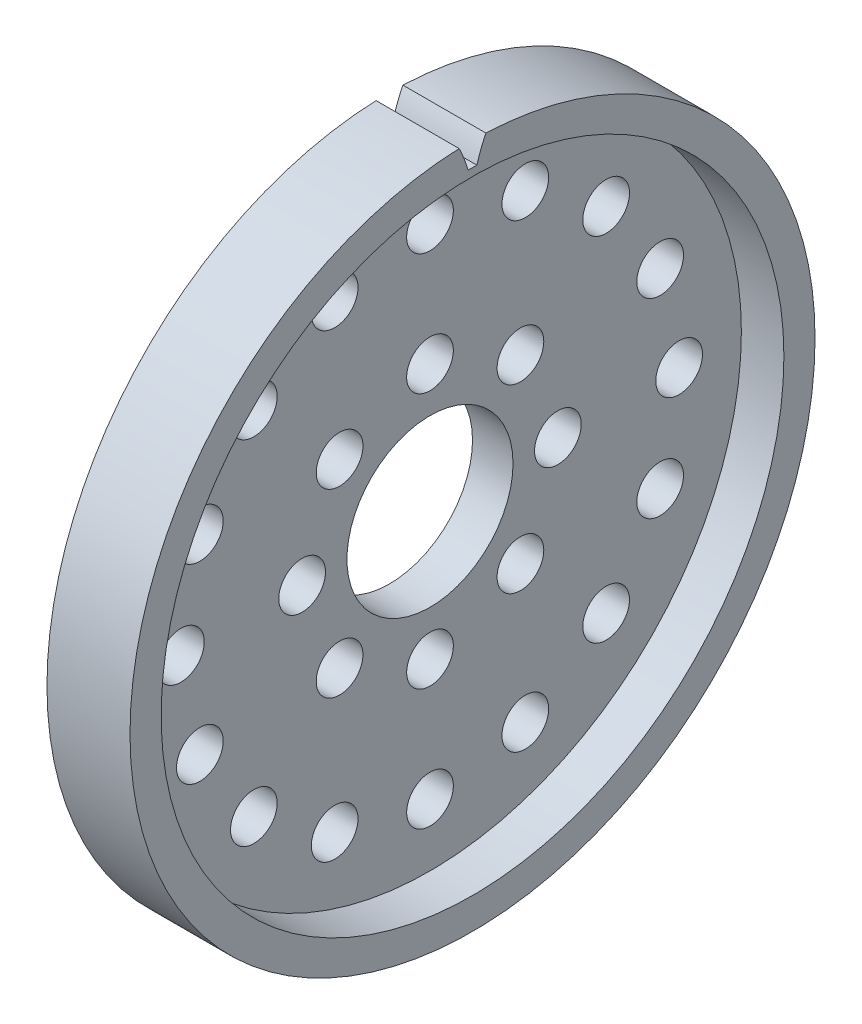
SolidWorks part; units mm, degrees
material "7075-O (SS)"
ref_plane "Plane1" through (0, 0, 0) normal (0, 0, 1) x (1, 0, 0)
ref_plane "Plane2" through (0, 0, 0) normal (0, 1, 0) x (1, 0, 0)
ref_plane "Plane3" through (0, 0, 0) normal (1, 0, 0) x (0, 0, -1)
sketch "HoldingSke" plane through (0, 0, 0) normal (0, 1, 0) x (1, 0, 0)
  line L0 (0, 0) -> (356.3081, -730.5398)
  line L1 (-15, 0) -> (100, 0) construction
  line L2 (0, 0) -> (-2.1039, 2.3779)
  line L3 (0, 0) -> (-11.863, 4.5341)
  line L4 (0, 0) -> (3.7858, 7.762)
  line L5 (0, 0) -> (-47.5972, -17.7524)
  line L6 (0, 0) -> (-5.2639, -3.5516)
  line L7 (-2.1039, 2.3779) -> (8.8308, 51.9871)
  line L8 (-76.2, 54.61) -> (-61.976, 54.61)
  line L9 (-71.009, 38.7566) -> (-53.1078, 45.2721)
  line L10 (-76.2, 71.12) -> (104.1128, 71.12)
  line L11 (0, 0) -> (-6.35, 0)
  line L12 (-76.2, 101.6) -> (-76.1716, 101.6)
  line L13 (24.9733, 27.94) -> (52.9518, 28.4284)
  line L14 (24.9733, 27.94) -> (25.0241, 27.9398)
  line L15 (24.9733, 27.94) -> (100.4021, 29.52)
  circle A0 centre (0, 0) radius 6.35
  circle A1 centre (0, 0) radius 24.3967
  circle A2 centre (0, 0) radius 38.1
  circle A3 centre (0, 0) radius 6.35
  dimension "MHD" = 48.7934
  dimension "Hub_dia" = 76.2
  dimension "Bore" = 12.7
  dimension "MBD" = 12.7
  dimension "Num_teeth" = 64
  dimension "Pitch_radius" = 180.3128
  dimension "Pitch" = 812.8
  dimension "Width" = 6.35
  dimension "Overall_len" = 50.8
  dimension "Show_teeth" = 64
  dimension "Thickness" = 6.35
  dimension "OAL" = 50.8001
  dimension "T_dim" = 14.224
  dimension "Ap" = 20
  dimension "H" = 19.05
  dimension "Backlash" = 0.0284
  dimension "Addendum_fac" = 1
  dimension "Dedendum_fac" = 1.2
  dimension "Clearance_fac" = 0.2
  dimension "Dedendum_add" = 0.0508
sketch "BasProSke" plane through (0, 0, 0) normal (0, 1, 0) x (1, 0, 0)
  line L0 (-10, 0) -> (60, 0) construction
  line L1 (0, 0) -> (0, 26.1937)
  line L2 (0, 0) -> (6.35, 0)
  line L3 (6.35, 0) -> (6.35, 26.1937)
  line L4 (6.35, 26.1937) -> (0, 26.1937)
  dimension "Diameter" = 52.3875
  dimension "Thickness" = 6.35
revolve "Base-Revolve" add sketch "BasProSke" angle 360 about L0
sketch "TooCutSke" plane through (0, 0, 0) normal (1, 0, 0) x (0, 0, -1)
  line L1 (0, 0) -> (0, 107) construction
  line L2 (0, 0) -> (-0.6731, 25.3911) construction
  line L3 (0, 0) -> (-2.492, 50.7259) construction
  line L4 (-0.6731, 25.3911) -> (-1.246, 25.3629) construction
  arc A0 (0.3337, 24.3944) -> (-0.3337, 24.3944) centre (0, 0) ccw
  arc A1 (1.0373, 26.1986) -> (-1.0373, 26.1986) centre (0, 0) ccw
  circle A2 centre (0, 0) radius 25.4 construction
  circle A3 centre (0, 0) radius 23.8682 construction
  arc A4 (-0.3337, 24.3944) -> (-1.0373, 26.1986) centre (-10.1082, 21.6221) ccw
  arc A5 (1.0373, 26.1986) -> (0.3337, 24.3944) centre (10.1082, 21.6221) ccw
  dimension "Root_dia" = 48.7934
  dimension "Overcut_dia" = 52.4383
  dimension "Pitch_dia" = 50.8
  dimension "Base_dia" = 47.7364
  dimension "Flank_rad" = 10.16
  dimension "Half_ang" = 2.813
  dimension "Half_CT" = 0.5736
extrude "ToothCut" cut sketch "TooCutSke" along normal through all
sketch "HubNeaOneSke" plane through (0, 0, 0) normal (-1, 0, 0) x (0, 0, 1)
  circle A0 centre (0, 0) radius 24.3967
  dimension "Diameter" = 48.7934
sketch "HubNeaBotSke" plane through (0, 0, 0) normal (-1, 0, 0) x (0, 0, 1)
  circle A0 centre (0, 0) radius 24.3967
  dimension "Diameter" = 48.7934
ref_plane "FarPln" through (6.35, 0, 0) normal (1, 0, 0) x (0, 0, -1)
sketch "HubFarSke" plane through (6.35, 0, 0) normal (1, 0, 0) x (0, 0, -1)
  circle A0 centre (0, 0) radius 24.3967
  dimension "Diameter" = 48.7934
sketch "BorSke" plane through (0, 0, 0) normal (1, 0, 0) x (0, 0, -1)
  circle A0 centre (0, 0) radius 6.35
  dimension "Diameter" = 12.7
extrude "Bore" cut sketch "BorSke" along normal mid plane 101.6001
sketch "KeySke" plane through (0, 0, 0) normal (1, 0, 0) x (0, 0, -1)
  line L0 (-1.5875, 0) -> (-1.5875, 7.874)
  line L1 (-1.5875, 7.874) -> (1.5875, 7.874)
  line L2 (1.5875, 7.874) -> (1.5875, 0)
  line L3 (0, 0) -> (0, 34) construction
  line L4 (-1.5875, 0) -> (1.5875, 0)
  dimension "Offset" = 7.874
  dimension "Width" = 3.175
sketch "Sketch1" plane through (6.35, 0, 0) normal (1, 0, 0) x (0, 0, -1)
  circle A0 centre (0, 0) radius 23.8125
  dimension "D1" = 47.625
extrude "Cut-Extrude1" cut sketch "Sketch1" against normal blind 3.2512
hole_wizard "9/64 (0.14063) Diameter Hole1" positions "Sketch3" profile "Sketch2" hole size "9/64" standard "Ansi Inch"
sketch "Sketch3" plane through (3.0988, 0, 0) normal (1, 0, 0) x (0, 0, -1)
  circle A0 centre (0, 0) radius 6.35 construction
  point P0 (0, 9.779)
  point P1 (0, 19.05)
  point P68 (7.2901, 17.5999)
  point P69 (13.4704, 13.4704)
  point P70 (17.5999, 7.2901)
  point P71 (19.05, 0)
  point P72 (17.5999, -7.2901)
  point P73 (13.4704, -13.4704)
  point P74 (7.2901, -17.5999)
  point P75 (0, -19.05)
  point P76 (-7.2901, -17.5999)
  point P77 (-13.4704, -13.4704)
  point P78 (-17.5999, -7.2901)
  point P79 (-19.05, 0)
  point P80 (-17.5999, 7.2901)
  point P81 (-13.4704, 13.4704)
  point P82 (-7.2901, 17.5999)
  point P87 (6.9148, 6.9148)
  point P88 (9.779, 0)
  point P89 (6.9148, -6.9148)
  point P90 (0, -9.779)
  point P91 (-6.9148, -6.9148)
  point P92 (-9.779, 0)
  point P93 (-6.9148, 6.9148)
  dimension "D1" = 9.779
  dimension "D2" = 19.05
  dimension "D3" = 16
  dimension "D4" = 8
sketch "Sketch2" plane through (3.0988, 9.779, 0) normal (0, 1, 0) x (0, 0, -1)
  line L0 (0, 0) -> (0, 10.5981)
  line L1 (0, 10.5981) -> (1.786, 9.525)
  line L2 (1.786, 9.525) -> (1.786, 0)
  line L5 (1.786, 0) -> (0, 0)
  line L10 (0, 10.5981) -> (-1.786, 9.525) construction
  line L11 (0, -6.35) -> (0, 107.95) construction
  dimension "Hole Dia." = 3.572
  dimension "Hole Depth" = 9.525
  dimension "Drill Angle" = 118
equation "' \"Pitch@HoldingSke\" = 4"
equation "' \"Num_teeth@HoldingSke\" = 12"
equation "' \"Ap@HoldingSke\" =  20"
equation "' \"Width@HoldingSke\" = 0.5"
equation "' \"Hub_dia@HoldingSke\"= 1"
equation "' \"Overall_len@HoldingSke\" = 1.0"
equation "' \"Bore@HoldingSke\" = 0.75"
equation "' \"T_dim@HoldingSke\" = 0.85"
equation "' \"Width@KeySke\" = 0.25"
equation "' \"Show_teeth@HoldingSke\" = 13"
equation "' \"Backlash@HoldingSke\" = 0.009"
equation "' \"Addendum_fac@HoldingSke\" = 1.0"
equation "' \"Dedendum_fac@HoldingSke\" = 1.25"
equation "' \"Dedendum_add@HoldingSke\" = 0.00005"
equation "' \"Clearance_fac@HoldingSke\" = 0.25"
equation "' \"Pitch@HoldingSke\" = 0.5"
equation "' \"Num_teeth@HoldingSke\" = 23"
equation "' \"Show_teeth@HoldingSke\" = 23"
equation "' \"Backlash@HoldingSke\" = 0.0375"
equation "\"Overcut_dia@TooCutSke\" = (\"Num_teeth@HoldingSke\" + 2 * \"Addendum_fac@HoldingSke\") / \"Pitch@HoldingSke\" + 0.002"
equation "\"Pitch_dia@TooCutSke\" = \"Num_teeth@HoldingSke\" / \"Pitch@HoldingSke\""
equation "\"Base_dia@TooCutSke\" = \"Num_teeth@HoldingSke\" / \"Pitch@HoldingSke\" * cos((\"Ap@HoldingSke\"  * 3.14159265 / 180))"
equation "\"Root_dia@TooCutSke\" = (\"Num_teeth@HoldingSke\" + 2) / \"Pitch@HoldingSke\" - 2 * (\"Addendum_fac@HoldingSke\" + \"Dedendum_fac@HoldingSke\") / \"Pitch@HoldingSke\" - \"Dedendum_add@HoldingSke\" * 2"
equation "\"Half_ang@TooCutSke\" = 180 / \"Num_teeth@HoldingSke\""
equation "\"Half_CT@TooCutSke\" = \"Num_teeth@HoldingSke\" / \"Pitch@HoldingSke\" * sin((3.14159265 / 2 / \"Num_teeth@HoldingSke\")) / 2 - 7 * \"Backlash@HoldingSke\" / 4"
equation "\"Flank_rad@TooCutSke\" = \"Num_teeth@HoldingSke\" / \"Pitch@HoldingSke\" / 5"
equation "\"Radius@RootFillets\" = \"Clearance_fac@HoldingSke\" / \"Pitch@HoldingSke\" + \"Dedendum_add@HoldingSke\""
equation "\"Break_rad@Breaks\" = 0.02 / \"Pitch@HoldingSke\""
equation "\"Thickness@HoldingSke\" = \"Width@HoldingSke\""
equation "\"OAL@HoldingSke\" = \"Thickness@HoldingSke\""
equation "\"MHD@HoldingSke\" = (\"Num_teeth@HoldingSke\" + 2) / \"Pitch@HoldingSke\" - 2 * (\"Addendum_fac@HoldingSke\" + \"Dedendum_fac@HoldingSke\")  / \"Pitch@HoldingSke\" - \"Dedendum_add@HoldingSke\" * 2"
equation "\"MBD@HoldingSke\" = (\"Num_teeth@HoldingSke\" + 2) / \"Pitch@HoldingSke\" - 2 * (\"Addendum_fac@HoldingSke\" + \"Dedendum_fac@HoldingSke\")  / \"Pitch@HoldingSke\" - \"Dedendum_add@HoldingSke\" * 2 - 0.002"
equation "\"MHD@HoldingSke\" = ((sgn( \"MHD@HoldingSke\" - \"Hub_dia@HoldingSke\" )-1)*( \"MHD@HoldingSke\" - \"Hub_dia@HoldingSke\" ))/-2+ \"Hub_dia@HoldingSke\""
equation "\"MBD@HoldingSke\" = ((sgn( \"MBD@HoldingSke\" - \"Bore@HoldingSke\" )-1)*( \"MBD@HoldingSke\" - \"Bore@HoldingSke\" ))/-2+ \"Bore@HoldingSke\""
equation "\"OAL@HoldingSke\" = ((sgn( \"OAL@HoldingSke\" - \"Overall_len@HoldingSke\" )+1)*( \"OAL@HoldingSke\" - \"Overall_len@HoldingSke\" ))/2 + \"Overall_len@HoldingSke\" + 0.000002"
equation "\"Num_teeth@TeethCuts\" = int( \"Show_teeth@HoldingSke\" ) + 1"
equation "\"Num_teeth@TeethCuts\" = ((sgn( \"Num_teeth@TeethCuts\" - \"Num_teeth@HoldingSke\" )-1)*( \"Num_teeth@TeethCuts\" - \"Num_teeth@HoldingSke\" ))/-2+ \"Num_teeth@HoldingSke\""
equation "\"Num_teeth@TeethCuts\" = ((sgn( \"Num_teeth@TeethCuts\" - 2.0)+1)*( \"Num_teeth@TeethCuts\" - 2.0))/2 +2.0"
equation "\"Angle@TeethCuts\" = 360.0 / \"Num_teeth@HoldingSke\""
equation "\"Diameter@BasProSke\" = (\"Num_teeth@HoldingSke\" + 2 * \"Addendum_fac@HoldingSke\") / \"Pitch@HoldingSke\""
equation "\"Thickness@BasProSke\"  = \"Thickness@HoldingSke\""
equation "' \"Fillet_rad@BasProSke\" =  \"Thickness@HoldingSke\" * 0.05"
equation "\"MHD@HoldingSke\" = ((sgn( \"MHD@HoldingSke\" - \"Root_dia@TooCutSke\" )-1)*( \"MHD@HoldingSke\" - \"Root_dia@TooCutSke\" ))/-2+ \"Root_dia@TooCutSke\""
equation "\"Diameter@HubNeaOneSke\" = \"MHD@HoldingSke\""
equation "\"Length@HubNearOne\" = \"OAL@HoldingSke\" - \"Thickness@BasProSke\""
equation "\"Diameter@HubNeaBotSke\" = \"MHD@HoldingSke\""
equation "\"Length@HubNearBoth\" = ( \"OAL@HoldingSke\" - \"Thickness@BasProSke\" ) / 2.0"
equation "\"Thickness@FarPln\" = \"Thickness@BasProSke\""
equation "\"Diameter@HubFarSke\" = \"MHD@HoldingSke\""
equation "\"Length@HubFar\" = ( \"OAL@HoldingSke\" - \"Thickness@BasProSke\" ) / 2.0"
equation "\"Diameter@BorSke\" = \"MBD@HoldingSke\""
equation "\"D1@Bore\" = \"OAL@HoldingSke\" * 2.0"
equation "\"D1@Keyway\" = \"OAL@HoldingSke\" * 2.0"
equation "\"Offset@KeySke\" = \"T_dim@HoldingSke\" - \"MBD@HoldingSke\" / 2.0"
